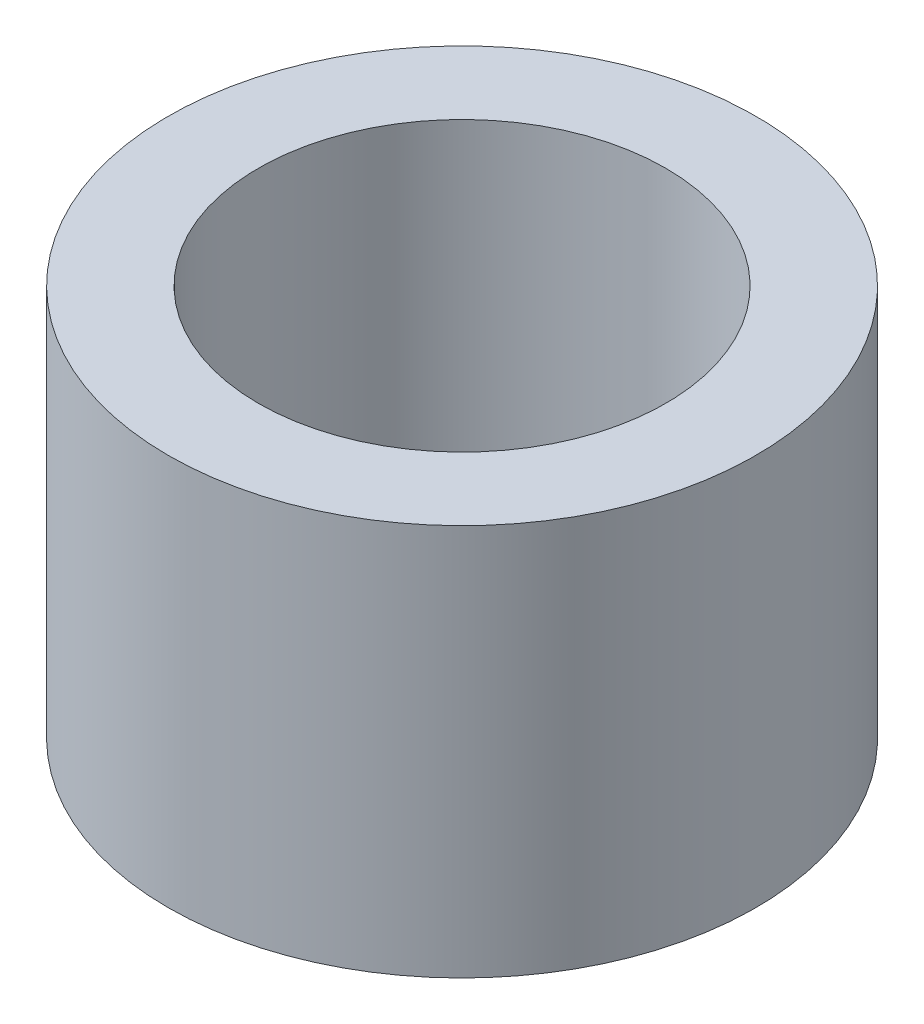
SolidWorks part; units mm, degrees
ref_plane "Front Plane" through (0, 0, 0) normal (0, 0, 1) x (1, 0, 0)
ref_plane "Top Plane" through (0, 0, 0) normal (0, 1, 0) x (1, 0, 0)
ref_plane "Right Plane" through (0, 0, 0) normal (1, 0, 0) x (0, 0, -1)
sketch "Sketch2" plane through (0, 0, 0) normal (0, 1, 0) x (1, 0, 0)
  circle A0 centre (0, 0) radius 4.7625
  circle A1 centre (0, 0) radius 3.302
  dimension "D1" = 9.525
  dimension "D2" = 6.604
extrude "Boss-Extrude1" add sketch "Sketch2" along normal blind 6.35
